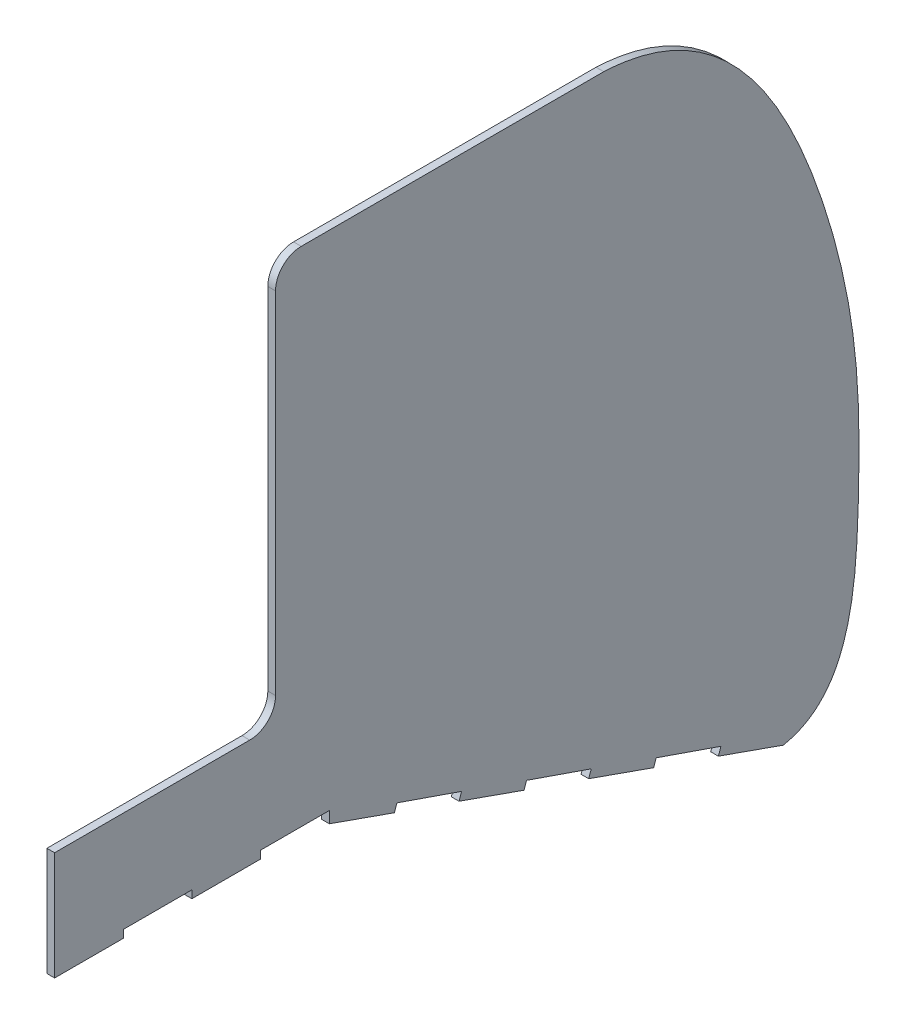
SolidWorks part; units mm, degrees
ref_plane "Front Plane" through (0, 0, 0) normal (0, 0, 1) x (1, 0, 0)
ref_plane "Top Plane" through (0, 0, 0) normal (0, 1, 0) x (1, 0, 0)
ref_plane "Right Plane" through (0, 0, 0) normal (1, 0, 0) x (0, 0, -1)
sketch "Sketch1" plane through (0, 0, 0) normal (1, 0, 0) x (0, 0, -1)
  line L5 (0, 0) -> (0, -59) construction
  line L6 (0, 0) -> (0, 196.9217) construction
  line L13 (-127.6733, 50.6216) -> (-127.6733, 186.9217)
  line L14 (-117.6733, 196.9217) -> (0, 196.9217)
  line L20 (-213.6, -1.5783) -> (-213.6, 40.6217)
  line L21 (-213.6, 40.6217) -> (-137.7211, 40.6217)
  line L57 (-106.7215, 1.4217) -> (-133.5, 1.4217)
  line L58 (-133.5, 1.4217) -> (-133.5, -1.5783)
  line L60 (-133.5, -1.5783) -> (-160.2, -1.5783)
  line L61 (-160.2, -1.5783) -> (-160.2, 1.4217)
  line L62 (-160.2, 1.4217) -> (-186.9, 1.4217)
  line L63 (-186.9, 1.4217) -> (-186.9, -1.5783)
  line L64 (-186.9, -1.5783) -> (-213.6, -1.5783)
  line L69 (-106.7215, 1.4217) -> (-106.7215, -3.0783)
  line L70 (-106.7215, -3.0783) -> (57.8709, -61.1762) construction
  line L71 (-106.7215, -3.0783) -> (-81.4531, -11.9975)
  line L72 (-81.4531, -11.9975) -> (-80.4723, -9.1624)
  line L73 (-56.2889, -20.7022) -> (-31.0205, -29.6214)
  line L74 (-31.0205, -29.6214) -> (-30.0397, -26.7863)
  line L75 (-5.8563, -38.3261) -> (19.4122, -47.2453)
  line L76 (19.4122, -47.2453) -> (20.3929, -44.4102)
  line L77 (44.5763, -55.95) -> (69.8448, -64.8692)
  line L79 (-80.4723, -9.1624) -> (-55.3082, -17.867)
  line L80 (-55.3082, -17.867) -> (-56.2889, -20.7022)
  line L81 (-30.0397, -26.7863) -> (-4.8756, -35.4909)
  line L82 (-4.8756, -35.4909) -> (-5.8563, -38.3261)
  line L83 (20.3929, -44.4102) -> (45.557, -53.1148)
  line L84 (45.557, -53.1148) -> (44.5763, -55.95)
  line L86 (69.8448, -64.8692) -> (70.8255, -62.0341) [skipped]
  arc A1 (-127.6733, 186.9217) -> (-117.6733, 196.9217) centre (-117.6733, 186.9217) cw
  arc A3 (-137.7211, 40.6217) -> (-127.6733, 50.6216) centre (-137.6733, 50.6216) ccw
  spline S0 degree 3 poles (0, 196.9217) (46.1968, 194.8557) (79.8849, 137.404) (99.1822, 59.2088) (100.053, 0.3036) (95.625, -59.9104) (69.8448, -64.8692) knots 0 0 0 0 0.394606 0.564234 0.764369 1 1 1 1
  dimension "D3" = 42.2
  dimension "D1" = 10
  dimension "D2" = 10
  dimension "D4" = 4
  dimension "D5" = 26.7
  dimension "D6" = 3
  dimension "D7" = 3
  dimension "D8" = 200
extrude "Boss-Extrude1" add sketch "Sketch1" along normal blind 3
